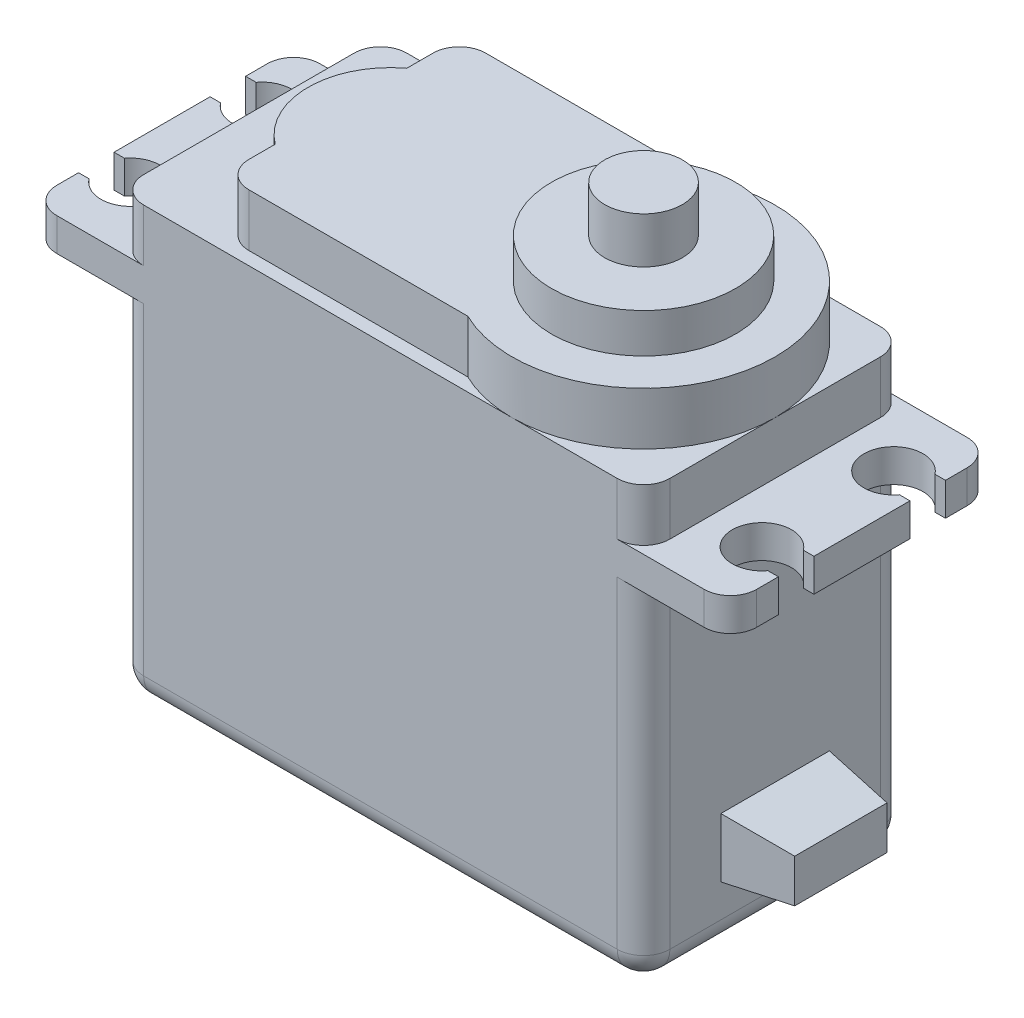
SolidWorks part; units mm, degrees
ref_plane "Front Plane" through (0, 0, 0) normal (0, 0, 1) x (1, 0, 0)
ref_plane "Top Plane" through (0, 0, 0) normal (0, 1, 0) x (1, 0, 0)
ref_plane "Right Plane" through (0, 0, 0) normal (1, 0, 0) x (0, 0, -1)
sketch "Sketch1" plane through (0, 0, 0) normal (0, 1, 0) x (1, 0, 0)
  line L0 (25.8, 6.35) -> (26.6, 6.35)
  line L1 (26.6, -10) -> (-26.6, -10)
  line L2 (26.6, -10) -> (26.6, 10)
  line L3 (26.6, 10) -> (-26.6, 10)
  line L4 (-26.6, -10) -> (-26.6, 10)
  line L5 (26.6, -10) -> (-26.6, 10) construction
  line L6 (26.6, 10) -> (-26.6, -10) construction
  line L7 (25.8, 3.65) -> (26.6, 3.65)
  line L8 (-55, 0) -> (55, 0) construction
  line L9 (25.8, -3.65) -> (26.6, -3.65)
  line L10 (25.8, -6.35) -> (26.6, -6.35)
  line L11 (0, -55) -> (0, 55) construction
  line L12 (-25.8, -6.35) -> (-26.6, -6.35)
  line L13 (-25.8, -3.65) -> (-26.6, -3.65)
  line L14 (-25.8, 3.65) -> (-26.6, 3.65)
  line L15 (-25.8, 6.35) -> (-26.6, 6.35)
  circle A0 centre (24, 5) radius 2.25
  circle A1 centre (24, -5) radius 2.25
  circle A2 centre (-24, -5) radius 2.25
  circle A3 centre (-24, 5) radius 2.25
  point P0 (0, 0)
  dimension "D3" = 24
  dimension "D5" = 4.5
  dimension "D1" = 53.2
  dimension "D2" = 20
  dimension "D4" = 5
  dimension "D6" = 2.7
extrude "Boss-Extrude1" add sketch "Sketch1" along normal blind 2.5 contours L15 A3 L14 L4 L13 A2 L12 L1 L2 L10 A1 L9 L7 A0 L0 L3
sketch "Sketch2" plane through (0, 2.5, 0) normal (0, 1, 0) x (1, 0, 0)
  line L0 (26.6, 10) -> (-26.6, 10) construction
  line L1 (20, -10) -> (-20, -10)
  line L2 (20, -10) -> (20, 10)
  line L3 (20, 10) -> (-20, 10)
  line L4 (-20, -10) -> (-20, 10)
  line L5 (20, -10) -> (-20, 10) construction
  line L6 (20, 10) -> (-20, -10) construction
  point P0 (0, 0)
  dimension "D1" = 40
extrude "Boss-Extrude2" add sketch "Sketch2" along normal blind 4
sketch "Sketch3" plane through (0, 0, 0) normal (0, -1, 0) x (1, 0, 0)
  line L0 (26.6, 10) -> (-26.6, 10) construction
  line L1 (20, -10) -> (-20, -10)
  line L2 (20, -10) -> (20, 10)
  line L3 (20, 10) -> (-20, 10)
  line L4 (-20, -10) -> (-20, 10)
  line L5 (20, -10) -> (-20, 10) construction
  line L6 (20, 10) -> (-20, -10) construction
  line L7 (20, 10) -> (20, -10) construction
  line L8 (20, 10) -> (20, -10)
  point P0 (0, 0)
extrude "Boss-Extrude3" add sketch "Sketch3" along normal blind 26.5 contours L2 L1 L4 L3
sketch "Sketch4" plane through (0, 6.5, 0) normal (0, 1, 0) x (1, 0, 0)
  line L0 (20, 10) -> (-20, 10) construction
  line L1 (20, -10) -> (20, 10) construction
  line L2 (5.6411, 9) -> (5.6411, -9)
  line L3 (-20, -10) -> (20, -10) construction
  line L4 (5.6411, 9) -> (-13, 9)
  line L5 (5.6411, -9) -> (-13, -9)
  line L6 (-13, -9) -> (-13, 9)
  line L7 (-13, 5) -> (-13, -5)
  circle A0 centre (10, 0) radius 10
  arc A1 (-13, -5) -> (-13, 5) centre (-9.25, 0) cw
  arc A2 (25.8, 6.35) -> (25.8, 3.65) centre (24, 5) ccw construction
  arc A3 (25.8, 6.35) -> (25.8, 3.65) centre (24, 5) ccw
  point P15 (-13, 0)
  point P17 (-15.5, 0)
  dimension "D1" = 1
  dimension "D2" = 23
  dimension "D3" = 2.5
  dimension "D4" = 10
extrude "Boss-Extrude4" add sketch "Sketch4" along normal blind 4 contours A0 L4 L6 L5 | L2 A0 | A0 L2 | A1 L6
sketch "Sketch5" plane through (0, 10.5, 0) normal (0, 1, 0) x (1, 0, 0)
  circle A0 centre (10, 0) radius 7
  arc A1 (5.6411, -9) -> (5.6411, 9) centre (10, 0) ccw construction
  dimension "D1" = 14
extrude "Boss-Extrude5" add sketch "Sketch5" along normal blind 3
sketch "Sketch6" plane through (0, 13.5, 0) normal (0, 1, 0) x (1, 0, 0)
  circle A0 centre (10, 0) radius 2.95
  dimension "D1" = 5.9
extrude "Boss-Extrude6" add sketch "Sketch6" along normal blind 3.5
fillet "Fillet1" radius 2 18 edges at (-20, -13.25, -10) (-20, 4.5, -10) (20, 4.5, -10) (20, -13.25, -10) (-20, -13.25, 10) (-20, 4.5, 10) (20, -13.25, 10) (20, 4.5, 10) (20, -26.5, 0) (0, -26.5, -10) (-20, -26.5, 0) (0, -26.5, 10) (26.6, 1.25, 10) (26.6, 1.25, -10) (-26.6, 1.25, -10) (-26.6, 1.25, 10) (-13, 8.5, -9) (-13, 8.5, 9)
sketch "Sketch7" plane through (20, 0, 0) normal (1, 0, 0) x (0, 0, -1)
  line L0 (8, -26.5) -> (-8, -26.5) construction
  line L1 (4.125, -22) -> (-4.125, -22)
  line L2 (4.125, -22) -> (4.125, -17.5)
  line L3 (4.125, -17.5) -> (-4.125, -17.5)
  line L4 (-4.125, -22) -> (-4.125, -17.5)
  line L5 (4.125, -22) -> (-4.125, -17.5) construction
  line L6 (4.125, -17.5) -> (-4.125, -22) construction
  line L7 (-8, -24.5) -> (8, -24.5) construction
  point P0 (0, -19.75)
  point P7 (0, -24.5)
  dimension "D1" = 4.5
  dimension "D2" = 8.25
  dimension "D3" = 4.5
extrude "Boss-Extrude7" add sketch "Sketch7" along normal blind 5
draft "Draft3" type of draft neutral plane draft angle 7 faces to draft 4 face at (22.5, -22, 0) face at (22.5, -19.75, 4.125) face at (22.5, -19.75, -4.125) face at (22.5, -17.5, 0) neutral plane through (20, -26.5, -10) neutral plane normal (1, 0, 0) parameters "D1"=7
